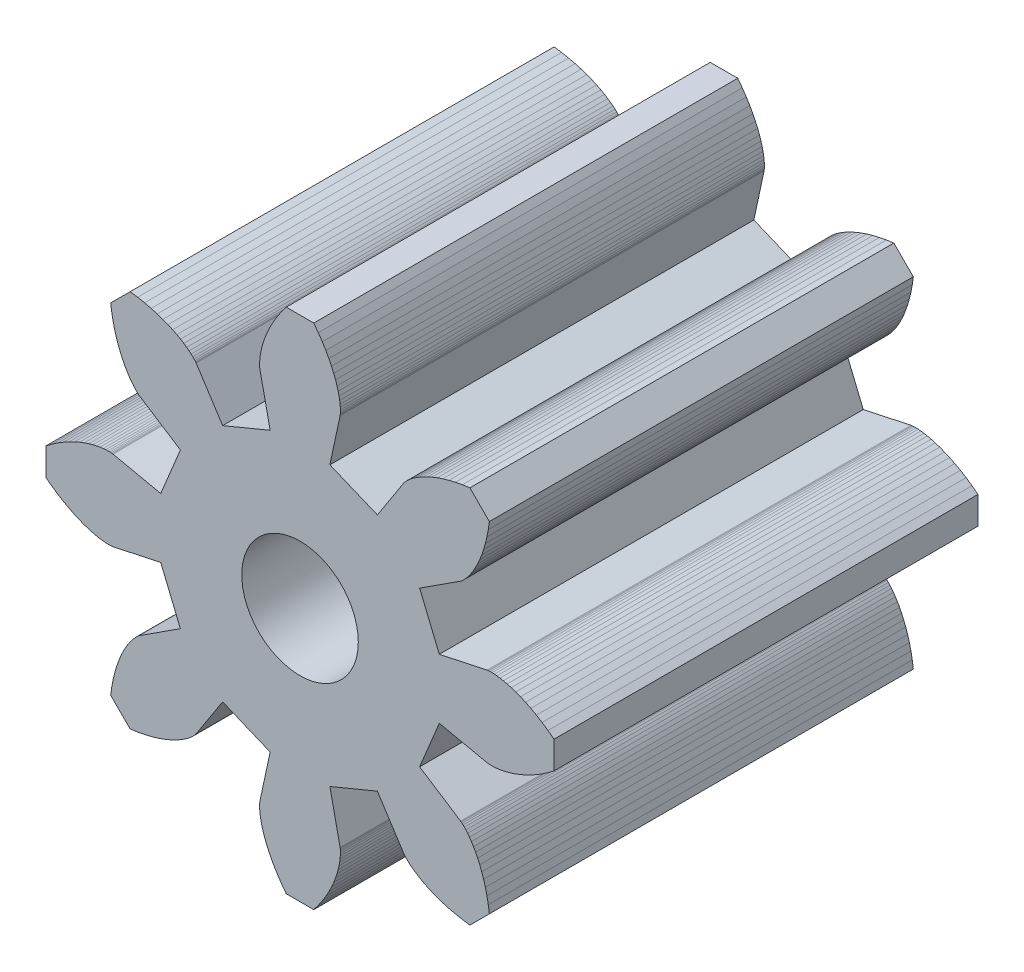
SolidWorks part; units mm, degrees
ref_plane "Front Plane" through (0, 0, 0) normal (0, 0, 1) x (1, 0, 0)
ref_plane "Top Plane" through (0, 0, 0) normal (0, 1, 0) x (1, 0, 0)
ref_plane "Right Plane" through (0, 0, 0) normal (1, 0, 0) x (0, 0, -1)
sketch "Model" plane through (0, 0, 0) normal (0, 0, 1) x (1, 0, 0)
  line L0 (3.9424, 0.8455) -> (5.2923, 1.135)
  line L1 (5.2923, 1.135) -> (5.298, 1.136)
  line L2 (5.298, 1.136) -> (5.3151, 1.1384)
  line L3 (5.3151, 1.1384) -> (5.3438, 1.1411)
  line L4 (5.3438, 1.1411) -> (5.3842, 1.1431)
  line L5 (5.3842, 1.1431) -> (5.4361, 1.1432)
  line L6 (5.4361, 1.1432) -> (5.4995, 1.1405)
  line L7 (5.4995, 1.1405) -> (5.5741, 1.1338)
  line L8 (5.5741, 1.1338) -> (5.6599, 1.1221)
  line L9 (5.6599, 1.1221) -> (5.7563, 1.1044)
  line L10 (5.7563, 1.1044) -> (5.8631, 1.0796)
  line L11 (5.8631, 1.0796) -> (5.9797, 1.0468)
  line L12 (5.9797, 1.0468) -> (6.1056, 1.0051)
  line L13 (6.1056, 1.0051) -> (6.2403, 0.9535)
  line L14 (6.2403, 0.9535) -> (6.383, 0.8911)
  line L15 (6.383, 0.8911) -> (6.533, 0.817)
  line L16 (6.533, 0.817) -> (6.6895, 0.7306)
  line L17 (6.6895, 0.7306) -> (6.8517, 0.631)
  line L18 (6.8517, 0.631) -> (7.0187, 0.5175)
  line L19 (7.0187, 0.5175) -> (7.1895, 0.3895)
  line L20 (7.1895, 0.3895) -> (7.1895, -0.3895)
  line L21 (7.1895, -0.3895) -> (7.0187, -0.5175)
  line L22 (7.0187, -0.5175) -> (6.8517, -0.631)
  line L23 (6.8517, -0.631) -> (6.6895, -0.7306)
  line L24 (6.6895, -0.7306) -> (6.533, -0.817)
  line L25 (6.533, -0.817) -> (6.383, -0.8911)
  line L26 (6.383, -0.8911) -> (6.2403, -0.9535)
  line L27 (6.2403, -0.9535) -> (6.1056, -1.0051)
  line L28 (6.1056, -1.0051) -> (5.9797, -1.0468)
  line L29 (5.9797, -1.0468) -> (5.8631, -1.0796)
  line L30 (5.8631, -1.0796) -> (5.7563, -1.1044)
  line L31 (5.7563, -1.1044) -> (5.6599, -1.1221)
  line L32 (5.6599, -1.1221) -> (5.5741, -1.1338)
  line L33 (5.5741, -1.1338) -> (5.4995, -1.1405)
  line L34 (5.4995, -1.1405) -> (5.4361, -1.1432)
  line L35 (5.4361, -1.1432) -> (5.3842, -1.1431)
  line L36 (5.3842, -1.1431) -> (5.3438, -1.1411)
  line L37 (5.3438, -1.1411) -> (5.3151, -1.1384)
  line L38 (5.3151, -1.1384) -> (5.298, -1.136)
  line L39 (5.298, -1.136) -> (5.2923, -1.135)
  line L40 (5.2923, -1.135) -> (3.9424, -0.8455)
  line L41 (3.9424, -0.8455) -> (3.3855, -2.1898)
  line L42 (3.3855, -2.1898) -> (4.5448, -2.9397)
  line L43 (4.5448, -2.9397) -> (4.5495, -2.943)
  line L44 (4.5495, -2.943) -> (4.5633, -2.9534)
  line L45 (4.5633, -2.9534) -> (4.5855, -2.9718)
  line L46 (4.5855, -2.9718) -> (4.6154, -2.9989)
  line L47 (4.6154, -2.9989) -> (4.6522, -3.0355)
  line L48 (4.6522, -3.0355) -> (4.6951, -3.0823)
  line L49 (4.6951, -3.0823) -> (4.7432, -3.1398)
  line L50 (4.7432, -3.1398) -> (4.7956, -3.2087)
  line L51 (4.7956, -3.2087) -> (4.8512, -3.2894)
  line L52 (4.8512, -3.2894) -> (4.9092, -3.3824)
  line L53 (4.9092, -3.3824) -> (4.9685, -3.4881)
  line L54 (4.9685, -3.4881) -> (5.0281, -3.6066)
  line L55 (5.0281, -3.6066) -> (5.0868, -3.7383)
  line L56 (5.0868, -3.7383) -> (5.1435, -3.8834)
  line L57 (5.1435, -3.8834) -> (5.1972, -4.0418)
  line L58 (5.1972, -4.0418) -> (5.2468, -4.2136)
  line L59 (5.2468, -4.2136) -> (5.291, -4.3987)
  line L60 (5.291, -4.3987) -> (5.3289, -4.597)
  line L61 (5.3289, -4.597) -> (5.3591, -4.8083)
  line L62 (5.3591, -4.8083) -> (4.8083, -5.3591)
  line L63 (4.8083, -5.3591) -> (4.597, -5.3289)
  line L64 (4.597, -5.3289) -> (4.3987, -5.291)
  line L65 (4.3987, -5.291) -> (4.2136, -5.2468)
  line L66 (4.2136, -5.2468) -> (4.0418, -5.1972)
  line L67 (4.0418, -5.1972) -> (3.8834, -5.1435)
  line L68 (3.8834, -5.1435) -> (3.7383, -5.0868)
  line L69 (3.7383, -5.0868) -> (3.6066, -5.0281)
  line L70 (3.6066, -5.0281) -> (3.4881, -4.9685)
  line L71 (3.4881, -4.9685) -> (3.3824, -4.9092)
  line L72 (3.3824, -4.9092) -> (3.2894, -4.8512)
  line L73 (3.2894, -4.8512) -> (3.2087, -4.7956)
  line L74 (3.2087, -4.7956) -> (3.1398, -4.7432)
  line L75 (3.1398, -4.7432) -> (3.0823, -4.6951)
  line L76 (3.0823, -4.6951) -> (3.0355, -4.6522)
  line L77 (3.0355, -4.6522) -> (2.9989, -4.6154)
  line L78 (2.9989, -4.6154) -> (2.9718, -4.5855)
  line L79 (2.9718, -4.5855) -> (2.9534, -4.5633)
  line L80 (2.9534, -4.5633) -> (2.943, -4.5495)
  line L81 (2.943, -4.5495) -> (2.9397, -4.5448)
  line L82 (2.9397, -4.5448) -> (2.1898, -3.3855)
  line L83 (2.1898, -3.3855) -> (0.8455, -3.9424)
  line L84 (0.8455, -3.9424) -> (1.135, -5.2923)
  line L85 (1.135, -5.2923) -> (1.136, -5.298)
  line L86 (1.136, -5.298) -> (1.1384, -5.3151)
  line L87 (1.1384, -5.3151) -> (1.1411, -5.3438)
  line L88 (1.1411, -5.3438) -> (1.1431, -5.3842)
  line L89 (1.1431, -5.3842) -> (1.1432, -5.4361)
  line L90 (1.1432, -5.4361) -> (1.1405, -5.4995)
  line L91 (1.1405, -5.4995) -> (1.1338, -5.5741)
  line L92 (1.1338, -5.5741) -> (1.1221, -5.6599)
  line L93 (1.1221, -5.6599) -> (1.1044, -5.7563)
  line L94 (1.1044, -5.7563) -> (1.0796, -5.8631)
  line L95 (1.0796, -5.8631) -> (1.0468, -5.9797)
  line L96 (1.0468, -5.9797) -> (1.0051, -6.1056)
  line L97 (1.0051, -6.1056) -> (0.9535, -6.2403)
  line L98 (0.9535, -6.2403) -> (0.8911, -6.383)
  line L99 (0.8911, -6.383) -> (0.817, -6.533)
  line L100 (0.817, -6.533) -> (0.7306, -6.6895)
  line L101 (0.7306, -6.6895) -> (0.631, -6.8517)
  line L102 (0.631, -6.8517) -> (0.5175, -7.0187)
  line L103 (0.5175, -7.0187) -> (0.3895, -7.1895)
  line L104 (0.3895, -7.1895) -> (-0.3895, -7.1895)
  line L105 (-0.3895, -7.1895) -> (-0.5175, -7.0187)
  line L106 (-0.5175, -7.0187) -> (-0.631, -6.8517)
  line L107 (-0.631, -6.8517) -> (-0.7306, -6.6895)
  line L108 (-0.7306, -6.6895) -> (-0.817, -6.533)
  line L109 (-0.817, -6.533) -> (-0.8911, -6.383)
  line L110 (-0.8911, -6.383) -> (-0.9535, -6.2403)
  line L111 (-0.9535, -6.2403) -> (-1.0051, -6.1056)
  line L112 (-1.0051, -6.1056) -> (-1.0468, -5.9797)
  line L113 (-1.0468, -5.9797) -> (-1.0796, -5.8631)
  line L114 (-1.0796, -5.8631) -> (-1.1044, -5.7563)
  line L115 (-1.1044, -5.7563) -> (-1.1221, -5.6599)
  line L116 (-1.1221, -5.6599) -> (-1.1338, -5.5741)
  line L117 (-1.1338, -5.5741) -> (-1.1405, -5.4995)
  line L118 (-1.1405, -5.4995) -> (-1.1432, -5.4361)
  line L119 (-1.1432, -5.4361) -> (-1.1431, -5.3842)
  line L120 (-1.1431, -5.3842) -> (-1.1411, -5.3438)
  line L121 (-1.1411, -5.3438) -> (-1.1384, -5.3151)
  line L122 (-1.1384, -5.3151) -> (-1.136, -5.298)
  line L123 (-1.136, -5.298) -> (-1.135, -5.2923)
  line L124 (-1.135, -5.2923) -> (-0.8455, -3.9424)
  line L125 (-0.8455, -3.9424) -> (-2.1898, -3.3855)
  line L126 (-2.1898, -3.3855) -> (-2.9397, -4.5448)
  line L127 (-2.9397, -4.5448) -> (-2.943, -4.5495)
  line L128 (-2.943, -4.5495) -> (-2.9534, -4.5633)
  line L129 (-2.9534, -4.5633) -> (-2.9718, -4.5855)
  line L130 (-2.9718, -4.5855) -> (-2.9989, -4.6154)
  line L131 (-2.9989, -4.6154) -> (-3.0355, -4.6522)
  line L132 (-3.0355, -4.6522) -> (-3.0823, -4.6951)
  line L133 (-3.0823, -4.6951) -> (-3.1398, -4.7432)
  line L134 (-3.1398, -4.7432) -> (-3.2087, -4.7956)
  line L135 (-3.2087, -4.7956) -> (-3.2894, -4.8512)
  line L136 (-3.2894, -4.8512) -> (-3.3824, -4.9092)
  line L137 (-3.3824, -4.9092) -> (-3.4881, -4.9685)
  line L138 (-3.4881, -4.9685) -> (-3.6066, -5.0281)
  line L139 (-3.6066, -5.0281) -> (-3.7383, -5.0868)
  line L140 (-3.7383, -5.0868) -> (-3.8834, -5.1435)
  line L141 (-3.8834, -5.1435) -> (-4.0418, -5.1972)
  line L142 (-4.0418, -5.1972) -> (-4.2136, -5.2468)
  line L143 (-4.2136, -5.2468) -> (-4.3987, -5.291)
  line L144 (-4.3987, -5.291) -> (-4.597, -5.3289)
  line L145 (-4.597, -5.3289) -> (-4.8083, -5.3591)
  line L146 (-4.8083, -5.3591) -> (-5.3591, -4.8083)
  line L147 (-5.3591, -4.8083) -> (-5.3289, -4.597)
  line L148 (-5.3289, -4.597) -> (-5.291, -4.3987)
  line L149 (-5.291, -4.3987) -> (-5.2468, -4.2136)
  line L150 (-5.2468, -4.2136) -> (-5.1972, -4.0418)
  line L151 (-5.1972, -4.0418) -> (-5.1435, -3.8834)
  line L152 (-5.1435, -3.8834) -> (-5.0868, -3.7383)
  line L153 (-5.0868, -3.7383) -> (-5.0281, -3.6066)
  line L154 (-5.0281, -3.6066) -> (-4.9685, -3.4881)
  line L155 (-4.9685, -3.4881) -> (-4.9092, -3.3824)
  line L156 (-4.9092, -3.3824) -> (-4.8512, -3.2894)
  line L157 (-4.8512, -3.2894) -> (-4.7956, -3.2087)
  line L158 (-4.7956, -3.2087) -> (-4.7432, -3.1398)
  line L159 (-4.7432, -3.1398) -> (-4.6951, -3.0823)
  line L160 (-4.6951, -3.0823) -> (-4.6522, -3.0355)
  line L161 (-4.6522, -3.0355) -> (-4.6154, -2.9989)
  line L162 (-4.6154, -2.9989) -> (-4.5855, -2.9718)
  line L163 (-4.5855, -2.9718) -> (-4.5633, -2.9534)
  line L164 (-4.5633, -2.9534) -> (-4.5495, -2.943)
  line L165 (-4.5495, -2.943) -> (-4.5448, -2.9397)
  line L166 (-4.5448, -2.9397) -> (-3.3855, -2.1898)
  line L167 (-3.3855, -2.1898) -> (-3.9424, -0.8455)
  line L168 (-3.9424, -0.8455) -> (-5.2923, -1.135)
  line L169 (-5.2923, -1.135) -> (-5.298, -1.136)
  line L170 (-5.298, -1.136) -> (-5.3151, -1.1384)
  line L171 (-5.3151, -1.1384) -> (-5.3438, -1.1411)
  line L172 (-5.3438, -1.1411) -> (-5.3842, -1.1431)
  line L173 (-5.3842, -1.1431) -> (-5.4361, -1.1432)
  line L174 (-5.4361, -1.1432) -> (-5.4995, -1.1405)
  line L175 (-5.4995, -1.1405) -> (-5.5741, -1.1338)
  line L176 (-5.5741, -1.1338) -> (-5.6599, -1.1221)
  line L177 (-5.6599, -1.1221) -> (-5.7563, -1.1044)
  line L178 (-5.7563, -1.1044) -> (-5.8631, -1.0796)
  line L179 (-5.8631, -1.0796) -> (-5.9797, -1.0468)
  line L180 (-5.9797, -1.0468) -> (-6.1056, -1.0051)
  line L181 (-6.1056, -1.0051) -> (-6.2403, -0.9535)
  line L182 (-6.2403, -0.9535) -> (-6.383, -0.8911)
  line L183 (-6.383, -0.8911) -> (-6.533, -0.817)
  line L184 (-6.533, -0.817) -> (-6.6895, -0.7306)
  line L185 (-6.6895, -0.7306) -> (-6.8517, -0.631)
  line L186 (-6.8517, -0.631) -> (-7.0187, -0.5175)
  line L187 (-7.0187, -0.5175) -> (-7.1895, -0.3895)
  line L188 (-7.1895, -0.3895) -> (-7.1895, 0.3895)
  line L189 (-7.1895, 0.3895) -> (-7.0187, 0.5175)
  line L190 (-7.0187, 0.5175) -> (-6.8517, 0.631)
  line L191 (-6.8517, 0.631) -> (-6.6895, 0.7306)
  line L192 (-6.6895, 0.7306) -> (-6.533, 0.817)
  line L193 (-6.533, 0.817) -> (-6.383, 0.8911)
  line L194 (-6.383, 0.8911) -> (-6.2403, 0.9535)
  line L195 (-6.2403, 0.9535) -> (-6.1056, 1.0051)
  line L196 (-6.1056, 1.0051) -> (-5.9797, 1.0468)
  line L197 (-5.9797, 1.0468) -> (-5.8631, 1.0796)
  line L198 (-5.8631, 1.0796) -> (-5.7563, 1.1044)
  line L199 (-5.7563, 1.1044) -> (-5.6599, 1.1221)
  line L200 (-5.6599, 1.1221) -> (-5.5741, 1.1338)
  line L201 (-5.5741, 1.1338) -> (-5.4995, 1.1405)
  line L202 (-5.4995, 1.1405) -> (-5.4361, 1.1432)
  line L203 (-5.4361, 1.1432) -> (-5.3842, 1.1431)
  line L204 (-5.3842, 1.1431) -> (-5.3438, 1.1411)
  line L205 (-5.3438, 1.1411) -> (-5.3151, 1.1384)
  line L206 (-5.3151, 1.1384) -> (-5.298, 1.136)
  line L207 (-5.298, 1.136) -> (-5.2923, 1.135)
  line L208 (-5.2923, 1.135) -> (-3.9424, 0.8455)
  line L209 (-3.9424, 0.8455) -> (-3.3855, 2.1898)
  line L210 (-3.3855, 2.1898) -> (-4.5448, 2.9397)
  line L211 (-4.5448, 2.9397) -> (-4.5495, 2.943)
  line L212 (-4.5495, 2.943) -> (-4.5633, 2.9534)
  line L213 (-4.5633, 2.9534) -> (-4.5855, 2.9718)
  line L214 (-4.5855, 2.9718) -> (-4.6154, 2.9989)
  line L215 (-4.6154, 2.9989) -> (-4.6522, 3.0355)
  line L216 (-4.6522, 3.0355) -> (-4.6951, 3.0823)
  line L217 (-4.6951, 3.0823) -> (-4.7432, 3.1398)
  line L218 (-4.7432, 3.1398) -> (-4.7956, 3.2087)
  line L219 (-4.7956, 3.2087) -> (-4.8512, 3.2894)
  line L220 (-4.8512, 3.2894) -> (-4.9092, 3.3824)
  line L221 (-4.9092, 3.3824) -> (-4.9685, 3.4881)
  line L222 (-4.9685, 3.4881) -> (-5.0281, 3.6066)
  line L223 (-5.0281, 3.6066) -> (-5.0868, 3.7383)
  line L224 (-5.0868, 3.7383) -> (-5.1435, 3.8834)
  line L225 (-5.1435, 3.8834) -> (-5.1972, 4.0418)
  line L226 (-5.1972, 4.0418) -> (-5.2468, 4.2136)
  line L227 (-5.2468, 4.2136) -> (-5.291, 4.3987)
  line L228 (-5.291, 4.3987) -> (-5.3289, 4.597)
  line L229 (-5.3289, 4.597) -> (-5.3591, 4.8083)
  line L230 (-5.3591, 4.8083) -> (-4.8083, 5.3591)
  line L231 (-4.8083, 5.3591) -> (-4.597, 5.3289)
  line L232 (-4.597, 5.3289) -> (-4.3987, 5.291)
  line L233 (-4.3987, 5.291) -> (-4.2136, 5.2468)
  line L234 (-4.2136, 5.2468) -> (-4.0418, 5.1972)
  line L235 (-4.0418, 5.1972) -> (-3.8834, 5.1435)
  line L236 (-3.8834, 5.1435) -> (-3.7383, 5.0868)
  line L237 (-3.7383, 5.0868) -> (-3.6066, 5.0281)
  line L238 (-3.6066, 5.0281) -> (-3.4881, 4.9685)
  line L239 (-3.4881, 4.9685) -> (-3.3824, 4.9092)
  line L240 (-3.3824, 4.9092) -> (-3.2894, 4.8512)
  line L241 (-3.2894, 4.8512) -> (-3.2087, 4.7956)
  line L242 (-3.2087, 4.7956) -> (-3.1398, 4.7432)
  line L243 (-3.1398, 4.7432) -> (-3.0823, 4.6951)
  line L244 (-3.0823, 4.6951) -> (-3.0355, 4.6522)
  line L245 (-3.0355, 4.6522) -> (-2.9989, 4.6154)
  line L246 (-2.9989, 4.6154) -> (-2.9718, 4.5855)
  line L247 (-2.9718, 4.5855) -> (-2.9534, 4.5633)
  line L248 (-2.9534, 4.5633) -> (-2.943, 4.5495)
  line L249 (-2.943, 4.5495) -> (-2.9397, 4.5448)
  line L250 (-2.9397, 4.5448) -> (-2.1898, 3.3855)
  line L251 (-2.1898, 3.3855) -> (-0.8455, 3.9424)
  line L252 (-0.8455, 3.9424) -> (-1.135, 5.2923)
  line L253 (-1.135, 5.2923) -> (-1.136, 5.298)
  line L254 (-1.136, 5.298) -> (-1.1384, 5.3151)
  line L255 (-1.1384, 5.3151) -> (-1.1411, 5.3438)
  line L256 (-1.1411, 5.3438) -> (-1.1431, 5.3842)
  line L257 (-1.1431, 5.3842) -> (-1.1432, 5.4361)
  line L258 (-1.1432, 5.4361) -> (-1.1405, 5.4995)
  line L259 (-1.1405, 5.4995) -> (-1.1338, 5.5741)
  line L260 (-1.1338, 5.5741) -> (-1.1221, 5.6599)
  line L261 (-1.1221, 5.6599) -> (-1.1044, 5.7563)
  line L262 (-1.1044, 5.7563) -> (-1.0796, 5.8631)
  line L263 (-1.0796, 5.8631) -> (-1.0468, 5.9797)
  line L264 (-1.0468, 5.9797) -> (-1.0051, 6.1056)
  line L265 (-1.0051, 6.1056) -> (-0.9535, 6.2403)
  line L266 (-0.9535, 6.2403) -> (-0.8911, 6.383)
  line L267 (-0.8911, 6.383) -> (-0.817, 6.533)
  line L268 (-0.817, 6.533) -> (-0.7306, 6.6895)
  line L269 (-0.7306, 6.6895) -> (-0.631, 6.8517)
  line L270 (-0.631, 6.8517) -> (-0.5175, 7.0187)
  line L271 (-0.5175, 7.0187) -> (-0.3895, 7.1895)
  line L272 (-0.3895, 7.1895) -> (0.3895, 7.1895)
  line L273 (0.3895, 7.1895) -> (0.5175, 7.0187)
  line L274 (0.5175, 7.0187) -> (0.631, 6.8517)
  line L275 (0.631, 6.8517) -> (0.7306, 6.6895)
  line L276 (0.7306, 6.6895) -> (0.817, 6.533)
  line L277 (0.817, 6.533) -> (0.8911, 6.383)
  line L278 (0.8911, 6.383) -> (0.9535, 6.2403)
  line L279 (0.9535, 6.2403) -> (1.0051, 6.1056)
  line L280 (1.0051, 6.1056) -> (1.0468, 5.9797)
  line L281 (1.0468, 5.9797) -> (1.0796, 5.8631)
  line L282 (1.0796, 5.8631) -> (1.1044, 5.7563)
  line L283 (1.1044, 5.7563) -> (1.1221, 5.6599)
  line L284 (1.1221, 5.6599) -> (1.1338, 5.5741)
  line L285 (1.1338, 5.5741) -> (1.1405, 5.4995)
  line L286 (1.1405, 5.4995) -> (1.1432, 5.4361)
  line L287 (1.1432, 5.4361) -> (1.1431, 5.3842)
  line L288 (1.1431, 5.3842) -> (1.1411, 5.3438)
  line L289 (1.1411, 5.3438) -> (1.1384, 5.3151)
  line L290 (1.1384, 5.3151) -> (1.136, 5.298)
  line L291 (1.136, 5.298) -> (1.135, 5.2923)
  line L292 (1.135, 5.2923) -> (0.8455, 3.9424)
  line L293 (0.8455, 3.9424) -> (2.1898, 3.3855)
  line L294 (2.1898, 3.3855) -> (2.9397, 4.5448)
  line L295 (2.9397, 4.5448) -> (2.943, 4.5495)
  line L296 (2.943, 4.5495) -> (2.9534, 4.5633)
  line L297 (2.9534, 4.5633) -> (2.9718, 4.5855)
  line L298 (2.9718, 4.5855) -> (2.9989, 4.6154)
  line L299 (2.9989, 4.6154) -> (3.0355, 4.6522)
  line L300 (3.0355, 4.6522) -> (3.0823, 4.6951)
  line L301 (3.0823, 4.6951) -> (3.1398, 4.7432)
  line L302 (3.1398, 4.7432) -> (3.2087, 4.7956)
  line L303 (3.2087, 4.7956) -> (3.2894, 4.8512)
  line L304 (3.2894, 4.8512) -> (3.3824, 4.9092)
  line L305 (3.3824, 4.9092) -> (3.4881, 4.9685)
  line L306 (3.4881, 4.9685) -> (3.6066, 5.0281)
  line L307 (3.6066, 5.0281) -> (3.7383, 5.0868)
  line L308 (3.7383, 5.0868) -> (3.8834, 5.1435)
  line L309 (3.8834, 5.1435) -> (4.0418, 5.1972)
  line L310 (4.0418, 5.1972) -> (4.2136, 5.2468)
  line L311 (4.2136, 5.2468) -> (4.3987, 5.291)
  line L312 (4.3987, 5.291) -> (4.597, 5.3289)
  line L313 (4.597, 5.3289) -> (4.8083, 5.3591)
  line L314 (4.8083, 5.3591) -> (5.3591, 4.8083)
  line L315 (5.3591, 4.8083) -> (5.3289, 4.597)
  line L316 (5.3289, 4.597) -> (5.291, 4.3987)
  line L317 (5.291, 4.3987) -> (5.2468, 4.2136)
  line L318 (5.2468, 4.2136) -> (5.1972, 4.0418)
  line L319 (5.1972, 4.0418) -> (5.1435, 3.8834)
  line L320 (5.1435, 3.8834) -> (5.0868, 3.7383)
  line L321 (5.0868, 3.7383) -> (5.0281, 3.6066)
  line L322 (5.0281, 3.6066) -> (4.9685, 3.4881)
  line L323 (4.9685, 3.4881) -> (4.9092, 3.3824)
  line L324 (4.9092, 3.3824) -> (4.8512, 3.2894)
  line L325 (4.8512, 3.2894) -> (4.7956, 3.2087)
  line L326 (4.7956, 3.2087) -> (4.7432, 3.1398)
  line L327 (4.7432, 3.1398) -> (4.6951, 3.0823)
  line L328 (4.6951, 3.0823) -> (4.6522, 3.0355)
  line L329 (4.6522, 3.0355) -> (4.6154, 2.9989)
  line L330 (4.6154, 2.9989) -> (4.5855, 2.9718)
  line L331 (4.5855, 2.9718) -> (4.5633, 2.9534)
  line L332 (4.5633, 2.9534) -> (4.5495, 2.943)
  line L333 (4.5495, 2.943) -> (4.5448, 2.9397)
  line L334 (4.5448, 2.9397) -> (3.3855, 2.1898)
  line L335 (3.3855, 2.1898) -> (3.9424, 0.8455)
sketch "Sketch4" plane through (-3.3855, 2.1898, 0) normal (0, 0, 1) x (1, 0, 0)
extrude "Boss-Extrude1" add sketch "Model" along normal mid plane 12
sketch "Sketch5" plane through (0, 0, 6) normal (0, 0, 1) x (1, 0, 0)
  circle A0 centre (0, 0) radius 1.65
  dimension "D1" = 3.3
extrude "Cut-Extrude1" cut sketch "Sketch5" against normal blind 10 contours A0
